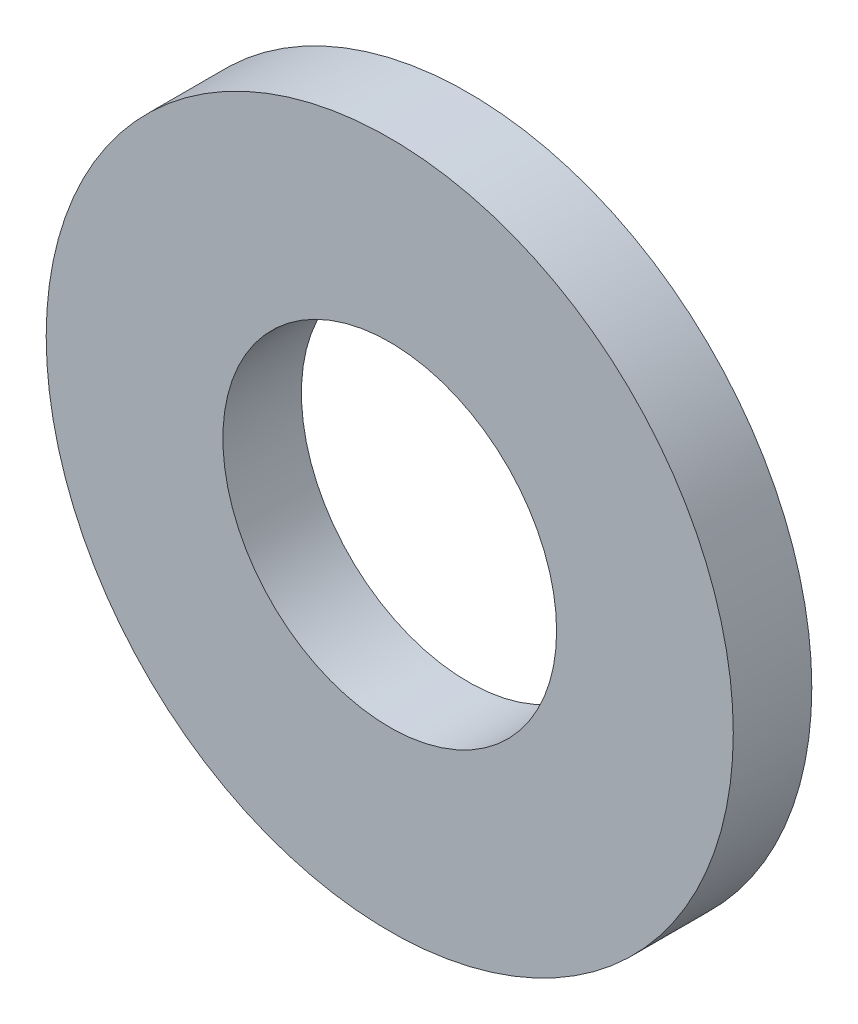
SolidWorks part; units mm, degrees
material "1.0036 (S235JRG1)"
ref_plane "Plan de face" through (0, 0, 0) normal (0, 0, 1) x (1, 0, 0)
ref_plane "Plan de dessus" through (0, 0, 0) normal (0, 1, 0) x (1, 0, 0)
ref_plane "Plan de droite" through (0, 0, 0) normal (1, 0, 0) x (0, 0, -1)
sketch "Esquisse1" plane through (0, 0, 0) normal (0, 0, 1) x (1, 0, 0)
  circle A0 centre (0, 0) radius 1.7
  circle A1 centre (0, 0) radius 3.5
  dimension "D1" = 3.4
  dimension "D2" = 7
extrude "Boss.-Extru.1" add sketch "Esquisse1" along normal blind 0.8
